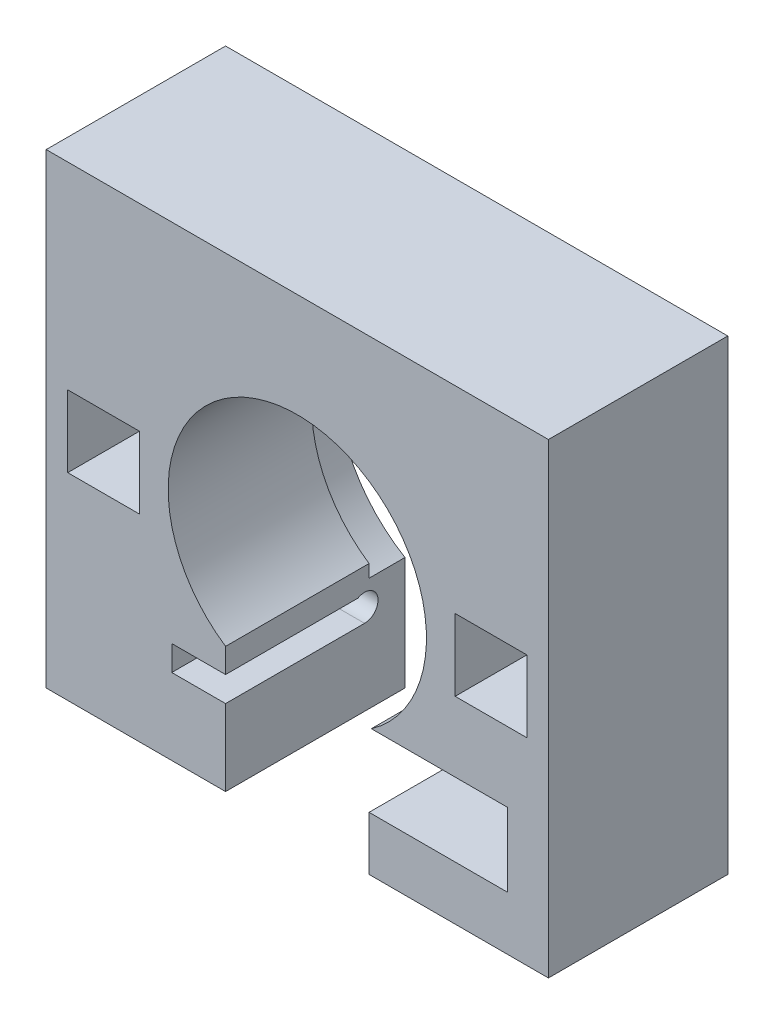
SolidWorks part; units mm, degrees
ref_plane "前基準面" through (0, 0, 0) normal (0, 0, 1) x (1, 0, 0)
ref_plane "上基準面" through (0, 0, 0) normal (0, 1, 0) x (1, 0, 0)
ref_plane "右基準面" through (0, 0, 0) normal (1, 0, 0) x (0, 0, -1)
sketch "草圖1" plane through (0, 0, 0) normal (0, 0, 1) x (1, 0, 0)
  line L1 (-61.4385, 56.9458) -> (78.5615, 56.9458)
  line L2 (-61.4385, 56.9458) -> (-61.4385, -73.0542)
  line L3 (-61.4385, -73.0542) -> (78.5615, -73.0542)
  line L4 (78.5615, 56.9458) -> (78.5615, -73.0542)
  line L5 (-55.4385, 1.9458) -> (-35.4385, 1.9458)
  line L6 (-55.4385, 1.9458) -> (-55.4385, -18.0542)
  line L7 (-55.4385, -18.0542) -> (-35.4385, -18.0542)
  line L8 (-35.4385, 1.9458) -> (-35.4385, -18.0542)
  line L9 (52.5615, 1.9458) -> (72.5615, 1.9458)
  line L10 (52.5615, 1.9458) -> (52.5615, -18.0542)
  line L11 (52.5615, -18.0542) -> (72.5615, -18.0542)
  line L12 (72.5615, 1.9458) -> (72.5615, -18.0542)
  circle A0 centre (8.5615, -8.0542) radius 36
  dimension "D9" = 72
  dimension "D12" = 65
  dimension "D13" = 70
  dimension "D1" = 140
  dimension "D2" = 130
  dimension "D3" = 6
  dimension "D4" = 6
  dimension "D5" = 20
  dimension "D6" = 20
  dimension "D7" = 20
  dimension "D8" = 20
  dimension "D10" = 55
  dimension "D11" = 55
extrude "填料-伸長1" add sketch "草圖1" along normal blind 50
sketch "草圖2" plane through (0, 0, 0) normal (0, 0, -1) x (-1, 0, 0)
  circle A0 centre (-8.5615, -8.0542) radius 39
  dimension "D1" = 78
extrude "除料-伸長1" cut sketch "草圖2" against normal blind 10
sketch "草圖3" plane through (0, -73.0542, 0) normal (0, -1, 0) x (1, 0, 0)
  line L0 (-61.4385, 50) -> (78.5615, 50) construction
  line L1 (-11.4385, 50) -> (28.5615, 50)
  line L2 (-11.4385, 50) -> (-11.4385, 0)
  line L3 (-11.4385, 0) -> (28.5615, 0)
  line L4 (28.5615, 50) -> (28.5615, 0)
  line L5 (-61.4385, 0) -> (78.5615, 0) construction
  line L6 (78.5615, 50) -> (78.5615, 0) construction
  dimension "D1" = 40
  dimension "D2" = 50
extrude "除料-伸長2" cut sketch "草圖3" against normal up to next
sketch "草圖4" plane through (-11.4385, 0, 0) normal (1, 0, 0) x (0, 0, -1)
  line L0 (-50, -37.9874) -> (-50, -73.0542) construction
  line L3 (-11.25, -51.8042) -> (-50, -51.8042)
  line L4 (-11.25, -51.8042) -> (-11.25, -44.8042)
  line L5 (-11.25, -44.8042) -> (-50, -44.8042)
  line L6 (-50, -51.8042) -> (-50, -44.8042)
  line L7 (0, -41.5355) -> (0, -73.0542) construction
  line L8 (-50, -73.0542) -> (0, -73.0542) construction
  circle A0 centre (-11.25, -48.0542) radius 3.75
  line M1 (-50, -37.9874) -> (-50, -73.0542)
  dimension "D1" = 11.25
  dimension "D2" = 7.5
  dimension "D3" = 25
  dimension "D4" = 21.25
  dimension "D5" = 7
extrude "除料-伸長3" cut sketch "草圖4" against normal blind 15 contours A0 L5 L3 M1
sketch "草圖6" plane through (0, 0, 50) normal (0, 0, 1) x (1, 0, 0)
  line L0 (28.5615, -37.9874) -> (28.5615, -73.0542) construction
  line L1 (28.5615, -37.5542) -> (38.2115, -37.5542)
  line L2 (28.5615, -37.5542) -> (28.5615, -58.0542)
  line L3 (28.5615, -58.0542) -> (38.2115, -58.0542)
  line L4 (38.2115, -37.5542) -> (38.2115, -58.0542)
  line L5 (28.5615, -73.0542) -> (78.5615, -73.0542) construction
  dimension "D1" = 15
  dimension "D2" = 20.5
  dimension "D3" = 9.65
extrude "除料-伸長4" cut sketch "草圖6" against normal through all
sketch "草圖7" plane through (0, 0, 50) normal (0, 0, 1) x (1, 0, 0)
  line L1 (38.2115, -37.5542) -> (67.2115, -37.5542)
  line L2 (38.2115, -37.5542) -> (38.2115, -58.0542)
  line L3 (38.2115, -58.0542) -> (67.2115, -58.0542)
  line L4 (67.2115, -37.5542) -> (67.2115, -58.0542)
  dimension "D1" = 29
  dimension "D2" = 20.5
extrude "除料-伸長5" cut sketch "草圖7" against normal blind 41
